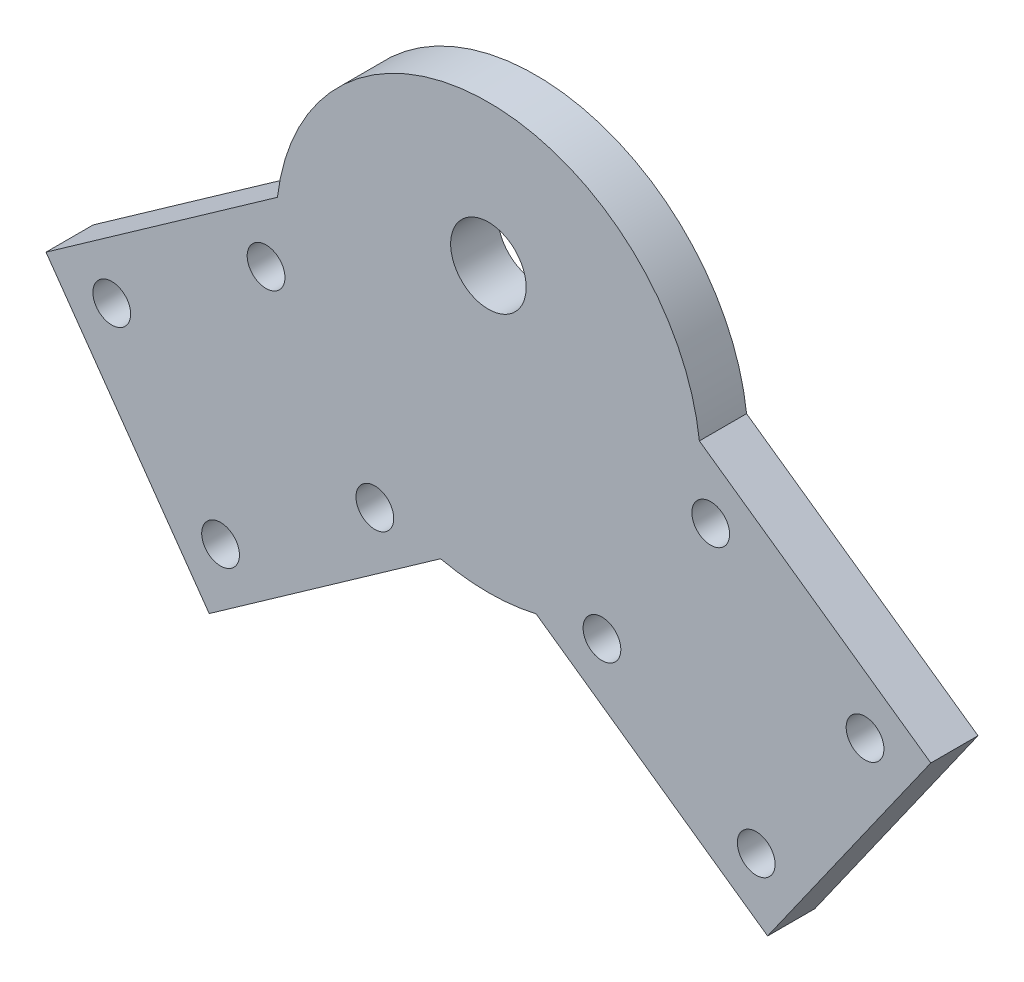
SolidWorks part; units mm, degrees
ref_plane "Front Plane" through (0, 0, 0) normal (0, 0, 1) x (1, 0, 0)
ref_plane "Top Plane" through (0, 0, 0) normal (0, 1, 0) x (1, 0, 0)
ref_plane "Right Plane" through (0, 0, 0) normal (1, 0, 0) x (0, 0, -1)
sketch "Sketch2" plane through (0, 0, 0) normal (0, 0, 1) x (1, 0, 0)
  line L8 (0, 0) -> (0, -22.5) construction
  line L9 (0, 0) -> (5.0614, -21.9233)
  line L10 (0, 0) -> (-5.0614, -21.9233)
  line L11 (5.0614, -21.9233) -> (22.35, 2.5941)
  line L12 (5.0614, -21.9233) -> (29.5789, -39.2119)
  line L13 (22.35, 2.5941) -> (46.8674, -14.6944)
  line L14 (29.5789, -39.2119) -> (46.8674, -14.6944)
  line L15 (-5.0614, -21.9233) -> (-22.35, 2.5941)
  line L16 (-5.0614, -21.9233) -> (-29.5789, -39.2119)
  line L17 (-22.35, 2.5941) -> (-46.8674, -14.6944)
  line L18 (-29.5789, -39.2119) -> (-46.8674, -14.6944)
  circle A0 centre (0, 0) radius 22.5
  dimension "D5" = 45
  dimension "D1" = 13
  dimension "D2" = 13
  dimension "D3" = 30
  dimension "D4" = 30
  dimension "D6" = 30
  dimension "D7" = 30
extrude "Boss-Extrude1" add sketch "Sketch2" along normal blind 5
sketch "Sketch4" plane through (0, 0, 5) normal (0, 0, 1) x (1, 0, 0)
  line L0 (-22.35, 2.5941) -> (-5.0614, -21.9233)
  line L1 (-22.35, 2.5941) -> (-46.8674, -14.6944) construction
  line L2 (-5.0614, -21.9233) -> (-29.5789, -39.2119) construction
  line L3 (-29.5789, -39.2119) -> (-46.8674, -14.6944) construction
  line L4 (5.0614, -21.9233) -> (22.35, 2.5941)
  line L7 (5.0614, -21.9233) -> (29.5789, -39.2119) construction
  line L8 (22.35, 2.5941) -> (46.8674, -14.6944) construction
  line L9 (29.5789, -39.2119) -> (46.8674, -14.6944) construction
  circle A0 centre (-39.8997, -15.8992) radius 2
  circle A1 centre (-23.5548, -4.3735) radius 2
  circle A2 centre (-12.0291, -20.7185) radius 2
  circle A3 centre (-28.374, -32.2442) radius 2
  circle A4 centre (23.5548, -4.3735) radius 2
  circle A6 centre (12.0291, -20.7185) radius 2
  circle A7 centre (39.8997, -15.8992) radius 2
  circle A8 centre (28.374, -32.2442) radius 2
  dimension "D10" = 4
  dimension "D11" = 4
  dimension "D12" = 4
  dimension "D13" = 4
  dimension "D19" = 4
  dimension "D20" = 4
  dimension "D25" = 4
  dimension "D26" = 4
  dimension "D1" = 30
  dimension "D2" = 5
  dimension "D3" = 5
  dimension "D4" = 5
  dimension "D5" = 5
  dimension "D6" = 5
  dimension "D7" = 5
  dimension "D8" = 5
  dimension "D9" = 5
  dimension "D14" = 30
  dimension "D15" = 5
  dimension "D16" = 5
  dimension "D17" = 5
  dimension "D18" = 5
  dimension "D21" = 5
  dimension "D22" = 5
  dimension "D23" = 5
  dimension "D24" = 5
extrude "Cut-Extrude1" cut sketch "Sketch4" against normal blind 10 contours A0 | A1 | A2 | A3 | A6 | A4 | A7 | A8
sketch "Sketch5" plane through (0, 0, 5) normal (0, 0, 1) x (1, 0, 0)
  line L0 (0, 22.5) -> (0, -22.5)
  arc A0 (22.35, 2.5941) -> (-22.35, 2.5941) centre (0, 0) ccw construction
  arc A1 (-5.0614, -21.9233) -> (5.0614, -21.9233) centre (0, 0) ccw construction
  circle A2 centre (0, 7.5) radius 4
  dimension "D2" = 8
  dimension "D1" = 15
extrude "Cut-Extrude2" cut sketch "Sketch5" against normal blind 10 contours A2
